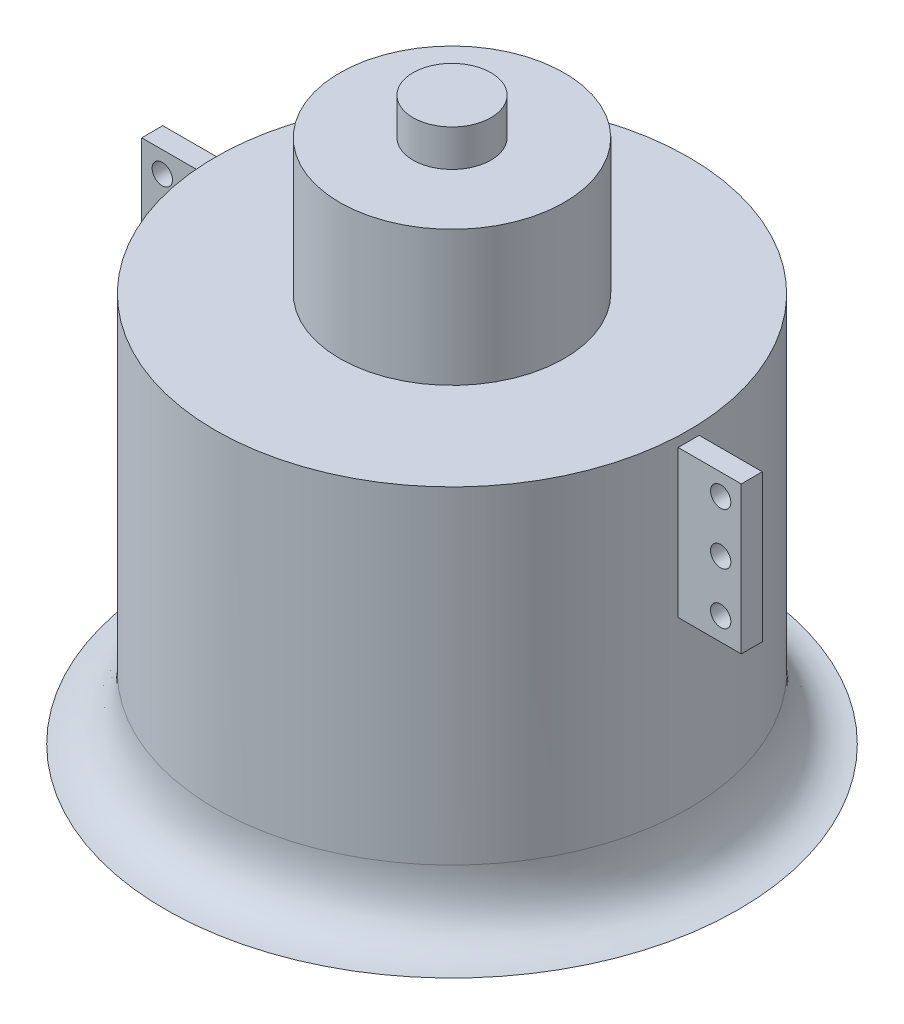
SolidWorks part; units mm, degrees
material "铸造合金钢"
ref_plane "Front" through (0, 0, 0) normal (0, 0, 1) x (1, 0, 0)
ref_plane "Top" through (0, 0, 0) normal (0, 1, 0) x (1, 0, 0)
ref_plane "Right" through (0, 0, 0) normal (1, 0, 0) x (0, 0, -1)
sketch "草图1" plane through (0, 0, 0) normal (0, 1, 0) x (1, 0, 0)
  circle A0 centre (0, 0) radius 45
extrude "凸台-拉伸1" add sketch "草图1" along normal blind 29.82
sketch "草图2" plane through (0, 0, 0) normal (0, 0, 1) x (1, 0, 0)
  line L0 (-45, 0) -> (-57, 0) construction
  line L1 (-57, 0) -> (-57, 28) construction
  line L2 (-57, 28) -> (-45, 28) construction
  line L3 (-45, 29.82) -> (-45, 0) construction
  line L4 (-45, 28) -> (-45, 0) construction
  line L5 (0, 29.82) -> (0, 0) construction
  line L6 (45, 29.82) -> (-45, 29.82) construction
  line L7 (45, 28) -> (45, 0) construction
  line L8 (45, 0) -> (57, 0) construction
  line L9 (57, 0) -> (57, 28) construction
  line L10 (57, 28) -> (45, 28) construction
  line L11 (57, 21.3561) -> (53.09, 21.3561) construction
  line L12 (53.09, 21.3561) -> (53.09, 28) construction
  line L13 (53.09, 28) -> (53.09, 23.97) construction
  line L14 (45, 28) -> (57, 28)
  line L15 (57, 28) -> (57, 0)
  line L16 (57, 0) -> (45, 0)
  line L17 (45, 0) -> (45, 28)
  line L18 (0, -50) -> (0, 50) construction
  line L19 (-57, 0) -> (-45, 0)
  line L20 (-45, 0) -> (-45, 28)
  line L21 (-57, 28) -> (-57, 0)
  line L22 (-45, 28) -> (-57, 28)
  line L23 (53.09, 28) -> (53.09, 14.145) construction
  line L24 (53.09, 28) -> (53.09, 4.33) construction
  circle A6 centre (53.09, 23.97) radius 1.93
  circle A7 centre (53.09, 14.145) radius 1.93
  circle A8 centre (53.09, 4.33) radius 1.93
  circle A9 centre (-53.09, 4.33) radius 1.93
  circle A10 centre (-53.09, 14.145) radius 1.93
  circle A11 centre (-53.09, 23.97) radius 1.93
extrude "凸台-拉伸2" add sketch "草图2" along normal mid plane 4 separate body
sketch "草图3" plane through (0, 29.82, 0) normal (0, 1, 0) x (1, 0, 0)
  circle A0 centre (0, 0) radius 21.35
extrude "凸台-拉伸3" add sketch "草图3" along normal blind 25.7
sketch "草图4" plane through (0, 55.52, 0) normal (0, 1, 0) x (1, 0, 0)
  circle A0 centre (0, 0) radius 7.41
extrude "凸台-拉伸4" add sketch "草图4" along normal blind 7
sketch "草图5" plane through (0, 0, 0) normal (0, -1, 0) x (1, 0, 0)
  circle A0 centre (0, 0) radius 45
extrude "凸台-拉伸5" add sketch "草图5" along normal blind 32.46
sketch "草图6" plane through (0, 0, 0) normal (0, 0, 1) x (1, 0, 0)
  line L0 (-45, -32.46) -> (-45, -44.34) construction
  line L1 (45, -32.46) -> (45, -44.34) construction
  line L2 (-45, -44.34) -> (-54.5, -44.34) construction
  line L4 (-45, -32.46) -> (-45, -44.34) construction
  line L5 (-45, -44.34) -> (-54.5, -44.34) construction
  line L10 (-54.5, -44.34) -> (0, -44.34)
  line L11 (0, -44.34) -> (0, -32.46)
  line L12 (-45, -32.46) -> (45, -32.46) construction
  line L13 (0, -32.46) -> (-45, -32.46)
  spline S0 degree 2 poles (-45, -32.46) (-45, -44.34) (-54.5, -44.34) knots 0 0 0 1 1 1
revolve "旋转1" add sketch "草图6" angle 360 about L11
